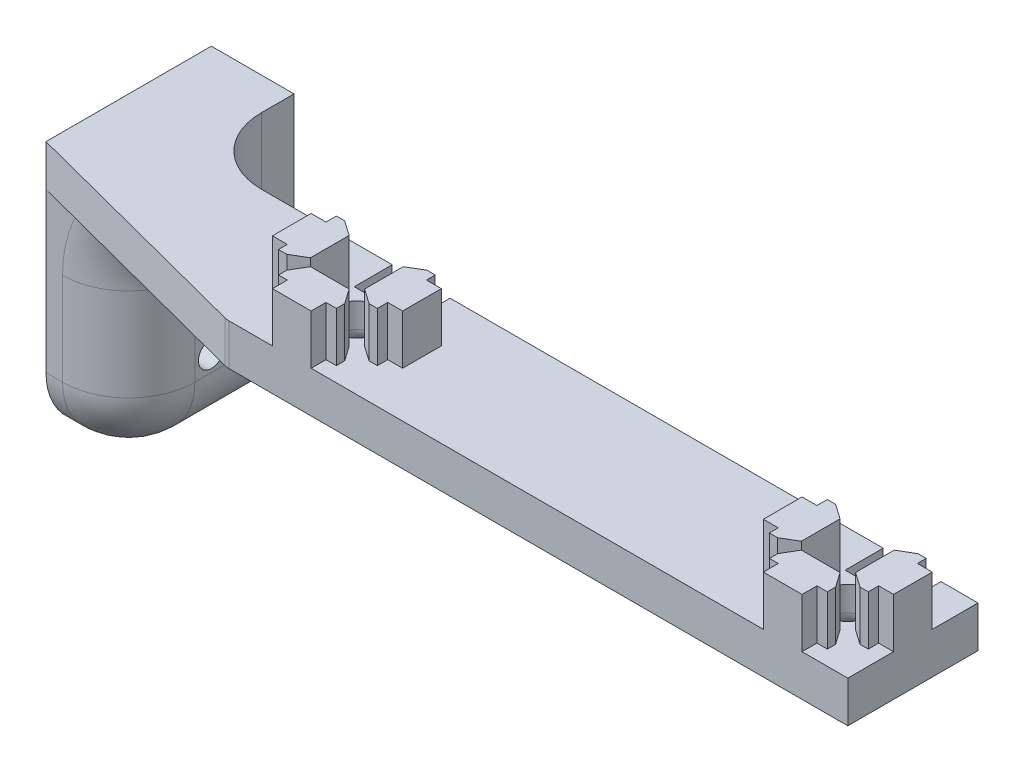
SolidWorks part; units mm, degrees
ref_plane "Front Plane" through (0, 0, 0) normal (0, 0, 1) x (1, 0, 0)
ref_plane "Top Plane" through (0, 0, 0) normal (0, 1, 0) x (1, 0, 0)
ref_plane "Right Plane" through (0, 0, 0) normal (1, 0, 0) x (0, 0, -1)
sketch "Sketch1" plane through (0, 0, 0) normal (0, 1, 0) x (1, 0, 0)
  line L0 (-2.9718, 10) -> (-2.9718, 7.714)
  line L1 (-10, 10) -> (10, 10)
  line L2 (-10, 10) -> (-10, -10)
  line L3 (-10, -10) -> (10, -10)
  line L4 (10, 10) -> (10, -10)
  line L5 (-10, 10) -> (10, -10) construction
  line L6 (-10, -10) -> (10, 10) construction
  line L7 (-2.9718, 10) -> (2.9718, 10) construction
  line L8 (-2.9718, 10) -> (-2.9718, 4.158) construction
  line L9 (-2.9718, 4.158) -> (2.9718, 4.158) construction
  line L10 (2.9718, 10) -> (2.9718, 4.158) construction
  line L11 (-4.5679, 7.714) -> (4.3221, 7.714) construction
  line L12 (-4.5679, 7.714) -> (-4.5679, 6.444) construction
  line L13 (-4.5679, 6.444) -> (4.3221, 6.444) construction
  line L14 (4.3221, 7.714) -> (4.3221, 6.444) construction
  line L15 (-4.5679, 7.714) -> (4.3221, 6.444) construction
  line L16 (-4.5679, 6.444) -> (4.3221, 7.714) construction
  line L17 (-2.9718, 7.714) -> (-4.5679, 7.714)
  line L18 (-4.5679, 7.714) -> (-4.5679, 6.444)
  line L19 (-4.5679, 6.444) -> (-2.9718, 4.158)
  line L20 (-2.9718, 4.158) -> (2.9718, 4.158)
  line L21 (2.9718, 4.158) -> (4.3221, 6.444)
  line L22 (4.3221, 6.444) -> (4.3221, 7.714)
  line L23 (4.3221, 7.714) -> (2.9718, 7.714)
  line L24 (2.9718, 7.714) -> (2.9718, 10)
  line L25 (2.9718, 10) -> (-2.9718, 10)
  line L26 (4.158, -2.9718) -> (4.158, 2.9718)
  line L27 (4.158, 2.9718) -> (6.444, 4.3221)
  line L28 (6.444, 4.3221) -> (7.714, 4.3221)
  line L29 (7.714, 4.3221) -> (7.714, 2.9718)
  line L30 (7.714, 2.9718) -> (10, 2.9718)
  line L31 (10, -2.9718) -> (10, 2.9718) construction
  line L32 (10, 2.9718) -> (10, -2.9718)
  line L33 (10, -2.9718) -> (7.714, -2.9718)
  line L34 (7.714, -2.9718) -> (7.714, -4.5679)
  line L35 (7.714, -4.5679) -> (6.444, -4.5679)
  line L36 (6.444, -4.5679) -> (4.158, -2.9718)
  line L37 (2.9718, -10) -> (-2.9718, -10) construction
  line L38 (4.5679, -6.444) -> (2.9718, -4.158)
  line L39 (4.5679, -7.714) -> (4.5679, -6.444)
  line L40 (2.9718, -7.714) -> (4.5679, -7.714)
  line L41 (2.9718, -10) -> (2.9718, -7.714)
  line L42 (-2.9718, -10) -> (2.9718, -10)
  line L43 (-2.9718, -7.714) -> (-2.9718, -10)
  line L44 (-4.3221, -7.714) -> (-2.9718, -7.714)
  line L45 (-4.3221, -6.444) -> (-4.3221, -7.714)
  line L46 (-2.9718, -4.158) -> (-4.3221, -6.444)
  line L47 (2.9718, -4.158) -> (-2.9718, -4.158)
  line L48 (-10, 2.9718) -> (-10, -2.9718) construction
  line L49 (-10, -2.9718) -> (-10, 2.9718)
  line L50 (-7.714, -2.9718) -> (-10, -2.9718)
  line L51 (-7.714, -4.3221) -> (-7.714, -2.9718)
  line L52 (-6.444, -4.3221) -> (-7.714, -4.3221)
  line L53 (-4.158, -2.9718) -> (-6.444, -4.3221)
  line L54 (-4.158, 2.9718) -> (-4.158, -2.9718)
  line L55 (-6.444, 4.5679) -> (-4.158, 2.9718)
  line L56 (-7.714, 4.5679) -> (-6.444, 4.5679)
  line L57 (-7.714, 2.9718) -> (-7.714, 4.5679)
  line L58 (-10, 2.9718) -> (-7.714, 2.9718)
  point P0 (0, 0)
  point P12 (0, 4.158)
  point P13 (-0.1229, 7.079)
  dimension "D1" = 20
  dimension "D2" = 20
  dimension "D4" = 5.9436
  dimension "D5" = 10
  dimension "D6" = 5.842
  dimension "D7" = 2.286
  dimension "D8" = 3.556
  dimension "D9" = 8.89
extrude "Boss-Extrude1" add sketch "Sketch1" along normal blind 7.62 contours L23 L24 L1 L0 L17 L18 L19 L20 L21 L22 | L26 L27 L28 L29 L30 L32 L33 L34 L35 L36 | L49 L58 L57 L56 L55 L54 L53 L52 L51 L50 | L38 L47 L46 L45 L44 L43 L42 L41 L40 L39
sketch "Sketch2" plane through (0, 0, 0) normal (0, -1, 0) x (1, 0, 0)
  line L1 (10, -10) -> (-122.9538, -10)
  line L2 (10, -10) -> (10, 10)
  line L3 (10, 10) -> (-122.9538, 10)
  line L4 (-122.9538, -10) -> (-122.9538, 10)
  line L5 (10, -10) -> (-122.9538, 10) construction
  line L6 (10, 10) -> (-122.9538, -10) construction
  line L7 (-2.9718, -10) -> (2.9718, -10) construction
  line L8 (10, -2.9718) -> (10, 2.9718) construction
  dimension "D1" = 132.9538
  dimension "D2" = 20
  dimension "D3" = 0
  dimension "D4" = 0
extrude "Boss-Extrude2" add sketch "Sketch2" along normal blind 6.35
pattern_linear "LPattern2" count 2 spacing 75.4126 along (-1, 0, 0) of "Boss-Extrude1"
sketch "Sketch4" plane through (0, -6.35, 0) normal (0, -1, 0) x (-1, 0, 0)
  line L0 (122.9538, 10) -> (122.9538, -0.2108) construction
  line L1 (122.9538, -10) -> (122.9538, 10) construction
  line L2 (122.9538, -10) -> (85.4126, -10)
  line L3 (-10, -10) -> (122.9538, -10) construction
  line L4 (85.4126, -10) -> (122.9538, -0.2108)
  line L5 (122.9538, -0.2108) -> (122.9538, -10)
  dimension "D1" = 10.2108
  dimension "D2" = 37.5412
extrude "Cut-Extrude1" cut sketch "Sketch4" against normal through all
fillet "Fillet1" radius 2.54 1 edges at (-85.4126, -3.175, 10)
sketch "Sketch13" plane through (0, 0, 0) normal (0, 1, 0) x (1, 0, 0)
  line L0 (-79.5706, -2.9718) -> (-81.8566, -4.3221) construction
  line L1 (4.158, 2.9718) -> (-4.158, 2.9718) construction
  line L2 (4.158, 2.9718) -> (4.158, -2.9718) construction
  line L3 (4.158, -2.9718) -> (-4.158, -2.9718) construction
  line L4 (-4.158, 2.9718) -> (-4.158, -2.9718) construction
  line L5 (-71.2546, 2.9718) -> (-79.5706, 2.9718) construction
  line L6 (-71.2546, 2.9718) -> (-71.2546, -2.9718) construction
  line L7 (-71.2546, -2.9718) -> (-79.5706, -2.9718) construction
  line L8 (-79.5706, 2.9718) -> (-79.5706, -2.9718) construction
  line L9 (-79.5706, 2.9718) -> (-79.5706, -2.9718) construction
  line L10 (-75.4126, 2.9718) -> (-75.4126, -2.9718) construction
  circle A0 centre (0, 0) radius 3.5
  circle A1 centre (-75.4126, 0) radius 3.5
  dimension "D1" = 7
  dimension "D2" = 7
extrude "Cut-Extrude5" cut sketch "Sketch13" against normal through all
fillet "Fillet6" radius 2.54 2 edges at (0, -6.35, 3.5) (-75.4126, -6.35, 3.5)
sketch "Sketch14" plane through (0, 7.62, 0) normal (0, 1, 0) x (1, 0, 0)
  line L0 (-78.3844, 4.158) -> (-72.4408, 4.158) construction
  line L5 (4.3221, 10) -> (-4.5679, 10)
  line L6 (4.3221, 10) -> (4.3221, 4.158)
  line L7 (4.3221, 4.158) -> (-4.5679, 4.158)
  line L8 (-4.5679, 10) -> (-4.5679, 4.158)
  line L9 (-71.0905, 4.158) -> (-79.9805, 4.158)
  line L10 (-71.0905, 4.158) -> (-71.0905, 10)
  line L11 (-71.0905, 10) -> (-79.9805, 10)
  line L12 (-79.9805, 4.158) -> (-79.9805, 10)
  line L13 (-71.0905, 4.158) -> (-79.9805, 10) construction
  line L14 (-71.0905, 10) -> (-79.9805, 4.158) construction
  line L15 (-78.3844, 10) -> (-72.4408, 10) construction
  line L16 (-79.9805, 7.714) -> (-79.9805, 6.444) construction
  line L17 (-71.0905, 6.444) -> (-71.0905, 7.714) construction
  line L18 (4.3221, 6.444) -> (4.3221, 7.714) construction
  line L19 (-4.5679, 7.714) -> (-4.5679, 6.444) construction
  point P0 (-75.5355, 7.079)
  point P19 (-79.9805, 7.079)
  dimension "D1" = 0
  dimension "D2" = 0
  dimension "D3" = 0
  dimension "D4" = 0
  dimension "D5" = 0
  dimension "D6" = 0
extrude "Cut-Extrude6" cut sketch "Sketch14" against normal through all
sketch "Sketch15" plane through (-122.9538, 0, 0) normal (-1, 0, 0) x (0, 0, 1)
  line L0 (0.2108, -6.35) -> (-10, -6.35) construction
  line L10 (0.2108, 0) -> (-25.1892, 0)
  line L11 (0.2108, 0) -> (0.2108, -40.894)
  line L12 (0.2108, -40.894) -> (-25.1892, -40.894)
  line L13 (-25.1892, 0) -> (-25.1892, -40.894)
  dimension "D1" = 34.544
  dimension "D2" = 25.4
extrude "Boss-Extrude3" add sketch "Sketch15" against normal blind 12.7
fillet "Fillet15" radius 10.16 1 edges at (-110.2538, -6.35, -4.8946)
fillet "Fillet16" radius 10.16 1 edges at (-110.2538, -8.255, -10)
fillet "Fillet17" radius 10.16 1 edges at (-110.2538, -40.894, -12.4892)
fillet "Fillet18" radius 10.16 4 edges at (-121.6838, -40.894, 0.2108) (-113.2296, -37.9182, 0.2108) (-107.278, -9.3258, 0.2108) (-110.2538, -23.622, 0.2108)
sketch "Sketch18" plane through (-122.9538, 0, 0) normal (-1, 0, 0) x (0, 0, 1)
  line L1 (-25.1892, -40.894) -> (-12.4892, -40.894) construction
  line L2 (-25.1892, -40.894) -> (-25.1892, -28.194) construction
  line L3 (-25.1892, -28.194) -> (-12.4892, -28.194) construction
  line L4 (-12.4892, -40.894) -> (-12.4892, -28.194) construction
  circle A0 centre (-12.4892, -28.194) radius 1.9844
  dimension "D3" = 3.9688
  dimension "D1" = 12.7
  dimension "D2" = 12.7
extrude "Cut-Extrude9" cut sketch "Sketch18" against normal up to surface (12.7 mm away) up to face at (-110.2538, -15.748, -18.4328)
